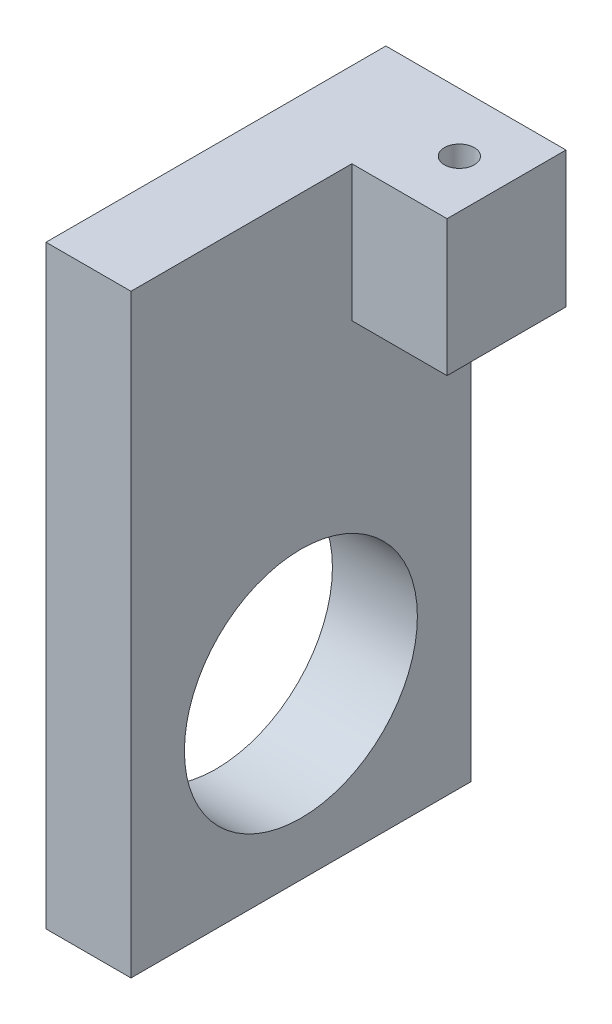
SolidWorks part; units mm, degrees
ref_plane "Front Plane" through (0, 0, 0) normal (0, 0, 1) x (1, 0, 0)
ref_plane "Top Plane" through (0, 0, 0) normal (0, 1, 0) x (1, 0, 0)
ref_plane "Right Plane" through (0, 0, 0) normal (1, 0, 0) x (0, 0, -1)
sketch "Sketch1" plane through (0, 0, -3.1935) normal (0, 0, 1) x (1, 0, 0)
  line L1 (-8.7255, -32.4424) -> (-2.3755, -32.4424)
  line L2 (-8.7255, -32.4424) -> (-8.7255, 12.0076)
  line L3 (-8.7255, 12.0076) -> (-2.3755, 12.0076)
  line L4 (-2.3755, -32.4424) -> (-2.3755, 12.0076)
  dimension "D1" = 6.35
  dimension "D2" = 44.45
extrude "Boss-Extrude1" add sketch "Sketch1" along normal blind 25.4
sketch "Sketch2" plane through (-2.3755, 0, 0) normal (1, 0, 0) x (0, 0, -1)
  line L1 (3.1935, 12.0076) -> (-5.6965, 12.0076)
  line L2 (3.1935, 12.0076) -> (3.1935, 1.8476)
  line L3 (3.1935, 1.8476) -> (-5.6965, 1.8476)
  line L4 (-5.6965, 12.0076) -> (-5.6965, 1.8476)
  dimension "D1" = 10.16
  dimension "D2" = 8.89
extrude "Boss-Extrude2" add sketch "Sketch2" along normal blind 7.112
sketch "Sketch3" plane through (-2.3755, 0, 0) normal (1, 0, 0) x (0, 0, -1)
  circle A0 centre (-9.5065, -19.7424) radius 8.7312 construction
  circle A1 centre (-9.5065, -19.7424) radius 8.7312
  circle A2 centre (-9.5065, -19.7424) radius 8.7058
  dimension "D1" = 0.0254
sketch "Sketch4" plane through (-2.3755, 0, 0) normal (1, 0, 0) x (0, 0, -1)
  circle A0 centre (-9.5065, -19.7424) radius 6.4416 construction
  circle A1 centre (-9.5065, -19.7424) radius 6.4416
extrude "Cut-Extrude1" cut sketch "Sketch4" against normal up to surface (6.35 mm away) up to face at (-8.7255, -10.2174, 9.5065)
extrude "Cut-Extrude2" cut sketch "Sketch3" against normal up to surface (6.35 mm away) contours A2
sketch "Sketch5" plane through (0, 12.0076, 0) normal (0, 1, 0) x (1, 0, 0)
  circle A0 centre (1.1551, -1.193) radius 0.9906 construction
  circle A1 centre (1.1551, -1.193) radius 0.9906
  circle A2 centre (1.1551, -1.193) radius 1.1176
  dimension "D1" = 0.127
extrude "Cut-Extrude3" cut sketch "Sketch5" against normal up to surface (10.16 mm away) contours A1 | A2 A1 up to face at (2.0695, 1.8476, 2.3627)
